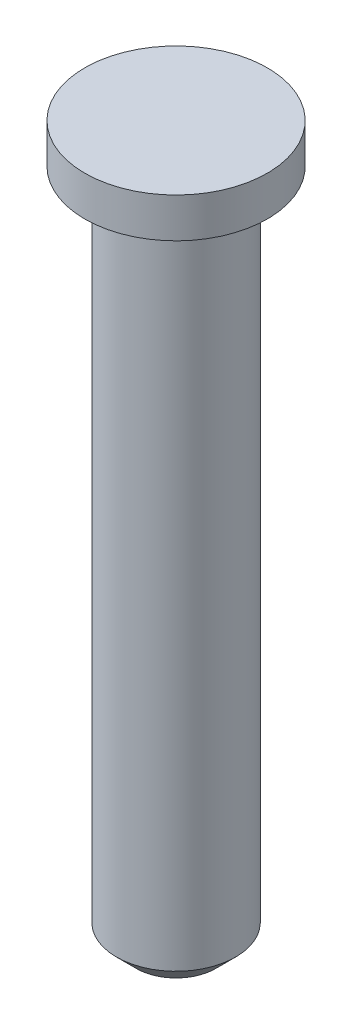
SolidWorks part; units mm, degrees
material "acero"
ref_plane "Alzado" through (0, 0, 0) normal (0, 0, 1) x (1, 0, 0)
ref_plane "Planta" through (0, 0, 0) normal (0, 1, 0) x (1, 0, 0)
ref_plane "Vista lateral" through (0, 0, 0) normal (1, 0, 0) x (0, 0, -1)
sketch "Croquis1" plane through (0, 0, 0) normal (0, 0, 1) x (1, 0, 0)
  line L0 (0, 0) -> (0, -60.9498) construction
  line L1 (0, 0) -> (2.3, 0)
  line L2 (2.3, 0) -> (2.3, -1)
  line L3 (2.3, -1) -> (1.5, -1)
  line L4 (1.5, -1) -> (1.5, -18)
  line L5 (1.5, -18) -> (0, -18)
  line L6 (0, -18) -> (0, 0)
  dimension "D1" = 18
  dimension "D2" = 1
  dimension "D3" = 4.6
  dimension "D4" = 3
revolve "Revolución1" add sketch "Croquis1" angle 360 about L0
chamfer "Chaflán1" distance 0.5 angle 45 1 edges at (0, -18, 1.5)
